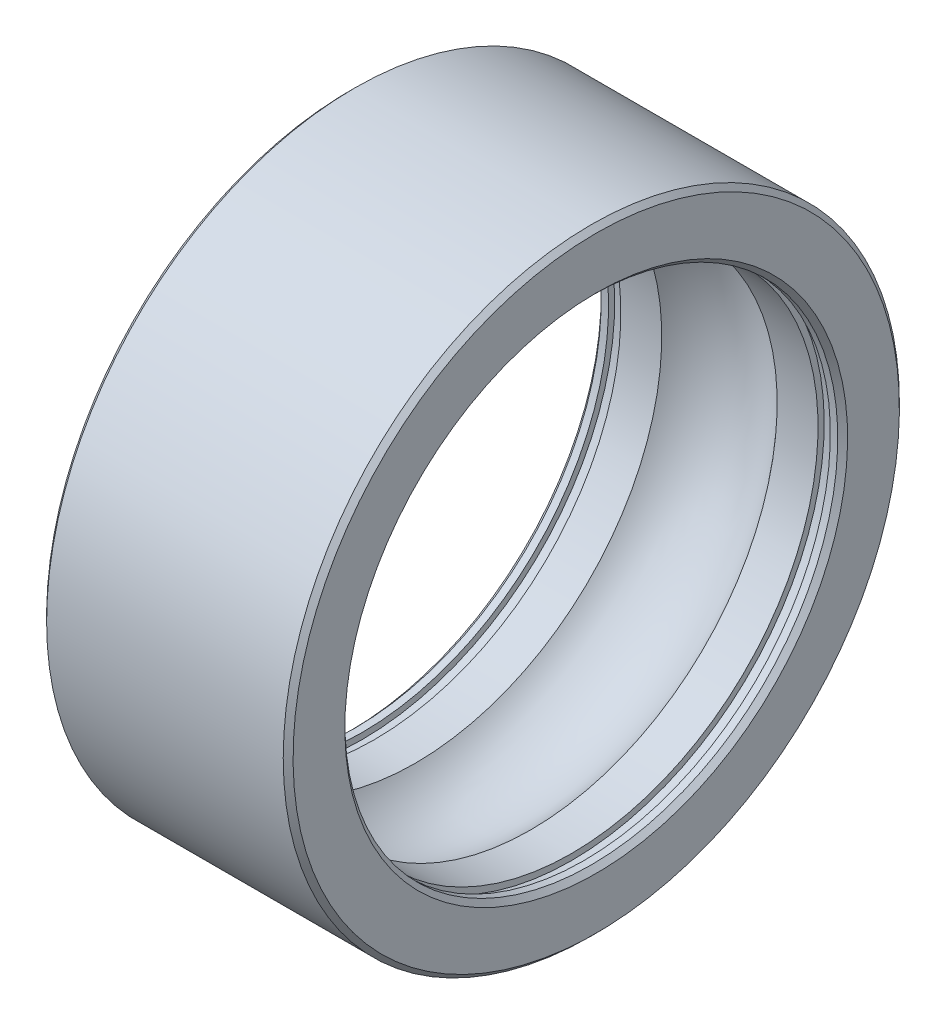
SolidWorks part; units mm, degrees
ref_plane "Front" through (0, 0, 0) normal (0, 0, 1) x (1, 0, 0)
ref_plane "Top" through (0, 0, 0) normal (0, 1, 0) x (1, 0, 0)
ref_plane "Right" through (0, 0, 0) normal (1, 0, 0) x (0, 0, -1)
sketch "Sketch1" plane through (0, 0, 0) normal (0, 0, 1) x (1, 0, 0)
  line L0 (-6.429, 0) -> (6.429, 0) construction
  line L1 (-2, -1.5) -> (2, -1.5) construction
  line L2 (-1.6, -4) -> (-0.9367, -4)
  line L3 (-2, -4) -> (-2, -5)
  line L4 (-2, -5) -> (2, -5)
  line L5 (2, -4) -> (2, -5)
  line L6 (0, -1.5) -> (0, -5) construction
  line L7 (-2, -2.6) -> (2, -2.6) construction
  line L8 (-1.6, -4) -> (-1.6, -4.1)
  line L9 (-1.6, -4.1) -> (-1.8, -4.1)
  line L10 (-1.8, -4.1) -> (-1.8, -4)
  line L11 (-1.8, -4) -> (-2, -4)
  line L12 (1.8, -4) -> (2, -4)
  line L13 (1.8, -4.1) -> (1.8, -4)
  line L14 (1.6, -4.1) -> (1.8, -4.1)
  line L15 (1.6, -4) -> (1.6, -4.1)
  line L16 (0.9367, -4) -> (1.6, -4)
  circle A0 centre (0, -3.25) radius 1.2 construction
  arc A1 (-0.9367, -4) -> (0.9367, -4) centre (0, -3.25) ccw
  point P13 (0, -3.25)
  point P15 (-1.8, -4.05)
  point P26 (0, 0)
  point P30 (0, -2.6)
  dimension "D3" = 2.4
  dimension "D1" = 5
  dimension "D2" = 1.5
  dimension "D4" = 2.6
  dimension "D5" = 4
  dimension "D6" = 0.4
  dimension "D7" = 4
  dimension "D8" = 0.1
  dimension "D9" = 0.2
  dimension "D11" = 4
revolve "Revolve1" add sketch "Sketch1" angle 360 about L0
chamfer "Chamfer1" distance 0.08 angle 45 4 edges at (2, -4, 0) (-2, -4, 0) (2, -5, 0) (-2, -5, 0)
